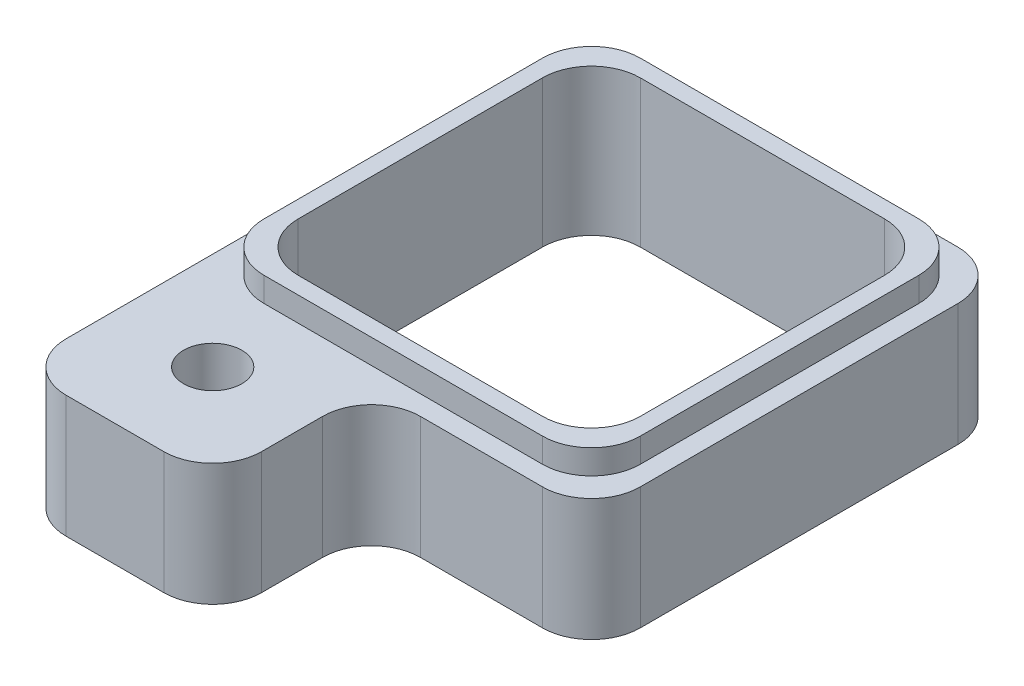
SolidWorks part; units mm, degrees
ref_plane "Front Plane" through (0, 0, 0) normal (0, 0, 1) x (1, 0, 0)
ref_plane "Top Plane" through (0, 0, 0) normal (0, 1, 0) x (1, 0, 0)
ref_plane "Right Plane" through (0, 0, 0) normal (1, 0, 0) x (0, 0, -1)
sketch "Sketch1" plane through (0, 0, 0) normal (0, 1, 0) x (1, 0, 0)
  line L1 (-4.25, -4.25) -> (4.25, -4.25)
  line L2 (-4.25, -4.25) -> (-4.25, 4.25)
  line L3 (-4.25, 4.25) -> (4.25, 4.25)
  line L4 (4.25, -4.25) -> (4.25, 4.25)
  line L5 (-4.25, -4.25) -> (4.25, 4.25) construction
  line L6 (-4.25, 4.25) -> (4.25, -4.25) construction
  point P0 (0, 0)
  dimension "D1" = 8.5
  dimension "D2" = 8.5
extrude "Extrude1" add sketch "Sketch1" along normal blind 2.5
sketch "Sketch15" plane through (0, 2.5, 0) normal (0, 1, 0) x (1, 0, 0)
  line L14 (-3.85, -3.85) -> (3.85, -3.85)
  line L15 (3.85, -3.85) -> (3.85, 3.85)
  line L16 (3.85, 3.85) -> (-3.85, 3.85)
  line L17 (-3.85, 3.85) -> (-3.85, -3.85)
  line L18 (-3.85, -3.85) -> (3.85, -3.85)
  line L19 (3.85, -3.85) -> (3.85, 3.85)
  line L20 (3.85, 3.85) -> (-3.85, 3.85)
  line L21 (-3.85, 3.85) -> (-3.85, -3.85)
  dimension "D1" = 0.4
extrude "Extrude8" add sketch "Sketch15" along normal blind 0.5
sketch "Sketch3" plane through (0, 0, 4.25) normal (0, 0, 1) x (1, 0, 0)
  line L0 (-4.25, 0) -> (4.25, 0) construction
  line L1 (-4.25, 2.5) -> (-0.25, 2.5)
  line L2 (-4.25, 2.5) -> (-4.25, 0)
  line L3 (-4.25, 0) -> (-0.25, 0)
  line L4 (-0.25, 2.5) -> (-0.25, 0)
  dimension "D1" = 4
extrude "Extrude3" add sketch "Sketch3" along normal blind 3.25
sketch "Sketch2" plane through (0, 2.5, 0) normal (0, 1, 0) x (1, 0, 0)
  line L1 (-3.5, -3.5) -> (3.5, -3.5)
  line L2 (-3.5, -3.5) -> (-3.5, 3.5)
  line L3 (-3.5, 3.5) -> (3.5, 3.5)
  line L4 (3.5, -3.5) -> (3.5, 3.5)
  line L5 (-3.5, -3.5) -> (3.5, 3.5) construction
  line L6 (-3.5, 3.5) -> (3.5, -3.5) construction
  point P0 (0, 0)
  dimension "D1" = 7
  dimension "D2" = 7
extrude "Extrude2" cut sketch "Sketch2" against normal through all and the other way through all
hole_wizard "#0-80 Tapped Hole1" positions "3DSketch2" profile "Sketch6" tap size "#0-80" standard "Ansi Inch" end condition through all
sketch3d "3DSketch2"
  line L0 (-0.25, 2.5, 7.5) -> (-4.25, 2.5, 7.5) construction
  line L1 (-0.25, 2.5, 7.5) -> (-0.25, 2.5, 4.25) construction
  point P0 (-2.25, 2.5, 5.5)
  dimension "D1" = 2
  dimension "D2" = 2
sketch "Sketch6" plane through (-2.25, 2.5, 5.5) normal (1, 0, 0) x (0, 0, 1)
  line L0 (0, 0) -> (0, 2.5001)
  line L1 (0, 2.5001) -> (0.5956, 2.5001)
  line L2 (0.5956, 2.5001) -> (0.5956, 0)
  line L5 (0.5956, 0) -> (0, 0)
  line L11 (0, -6.35) -> (0, 107.95) construction
  dimension "Thread Major Dia." = 1.1913
  dimension "Thru Tap Drill Depth" = 2.5001
sketch "Sketch11" plane through (0, 0, -4.25) normal (0, 0, -1) x (-1, 0, 0)
  line L0 (-4.25, 0) -> (4.25, 0) construction
  line L1 (-1.4296, 1) -> (0.5704, 1)
  line L2 (-1.4296, 1) -> (-1.4296, 0)
  line L3 (-1.4296, 0) -> (0.5704, 0)
  line L4 (0.5704, 1) -> (0.5704, 0)
  line L5 (-1.4296, 1) -> (0.5704, 0) construction
  line L6 (-1.4296, 0) -> (0.5704, 1) construction
  point P0 (-0.4296, 0.5)
  dimension "D1" = 0.5
  dimension "D2" = 2
extrude "Extrude5" add sketch "Sketch11" along normal blind 1.5
fillet "Fillet1" radius 1 14 edges at (3.5, 1.5, -3.5) (-3.5, 1.5, -3.5) (-3.5, 1.5, 3.5) (3.5, 1.5, 3.5) (-4.25, 1.25, 7.5) (-0.25, 1.25, 7.5) (4.25, 1.25, 4.25) (4.25, 1.25, -4.25) (-4.25, 1.25, -4.25) (-3.85, 2.75, 3.85) (-3.85, 2.75, -3.85) (3.85, 2.75, -3.85) (3.85, 2.75, 3.85)
